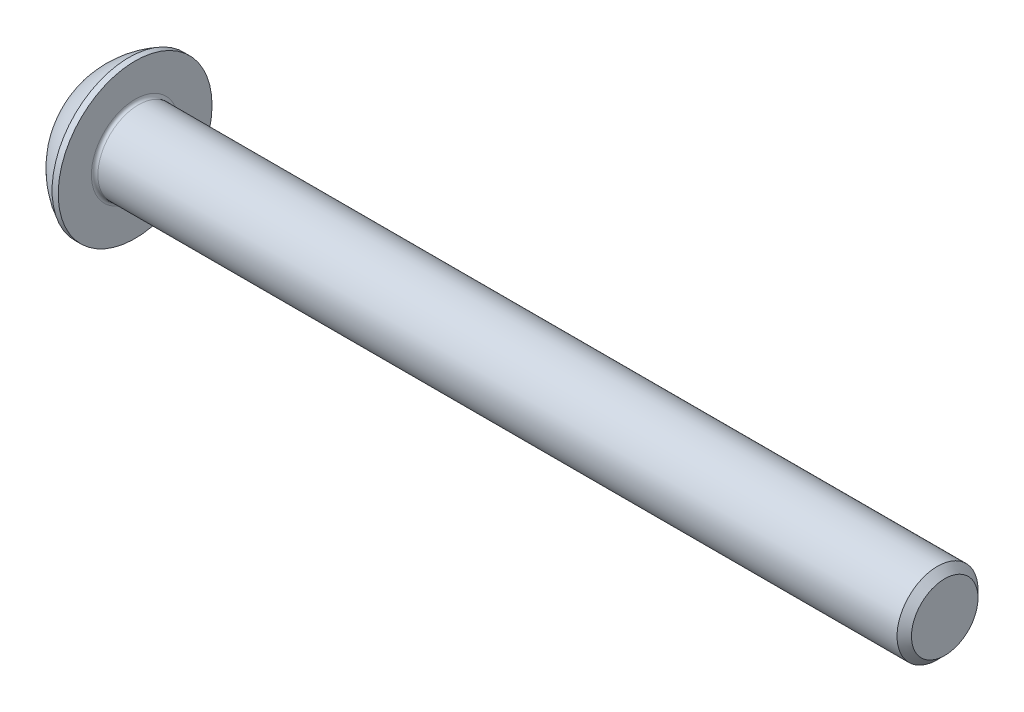
SolidWorks part; units mm, degrees
material "AISI 304"
ref_plane "Спереди" through (0, 0, 0) normal (0, 0, 1) x (1, 0, 0)
ref_plane "Сверху" through (0, 0, 0) normal (0, 1, 0) x (1, 0, 0)
ref_plane "Справа" through (0, 0, 0) normal (1, 0, 0) x (0, 0, -1)
sketch "Эскиз1" plane through (0, 0, 0) normal (0, 0, 1) x (1, 0, 0)
  line L0 (-3.6435, 0) -> (-10.508, 0) construction
  line L1 (0, 2.375) -> (0, 0)
  line L2 (0, 0) -> (52.75, 0)
  line L3 (52.75, 0) -> (52.75, 2.055)
  line L4 (52.75, 2.055) -> (52.305, 2.5)
  line L5 (52.305, 2.5) -> (2.75, 2.5)
  line L6 (2.75, 2.5) -> (2.75, 4.75)
  line L7 (2.75, 4.75) -> (2.3702, 4.75)
  arc A0 (2.3702, 4.75) -> (0, 2.375) centre (4.7549, 0) ccw
  dimension "D1" = 10.63
  dimension "D2" = 4.75
  dimension "D3" = 2.75
  dimension "D4" = 5
  dimension "D5" = 45
  dimension "D6" = 4.11
  dimension "D7" = 50
  dimension "D8" = 9.5
revolve "Body" add sketch "Эскиз1" angle 360 about L0
fillet "Скругление1" radius 0.2 1 edges at (2.75, 0, -2.5)
sketch "Эскиз2" plane through (0, 0, 0) normal (0, 0, 1) x (1, 0, 0)
  line L0 (0, 0) -> (0, 1.5)
  line L1 (0, 2.375) -> (0, -2.375) construction
  line L2 (0, 1.5) -> (1.56, 1.5)
  line L3 (1.56, 1.5) -> (2.426, 0)
  line L4 (2.426, 0) -> (0, 0)
  dimension "D1" = 1.56
  dimension "D2" = 60
  dimension "D3" = 1.5
revolve "Вырез-Повернуть1" cut sketch "Эскиз2" angle 360 about L4
sketch "Эскиз3" plane through (0, 0, 0) normal (-1, 0, 0) x (0, 0, 1)
  line L1 (-1.5, -0.866) -> (0, -1.7321)
  line L2 (0, -1.7321) -> (1.5, -0.866)
  line L3 (1.5, -0.866) -> (1.5, 0.866)
  line L4 (1.5, 0.866) -> (0, 1.7321)
  line L5 (0, 1.7321) -> (-1.5, 0.866)
  line L6 (-1.5, 0.866) -> (-1.5, -0.866)
  circle A0 centre (0, 0) radius 1.5 construction
  dimension "D1" = 3
extrude "Hex" cut sketch "Эскиз3" against normal blind 1.56
